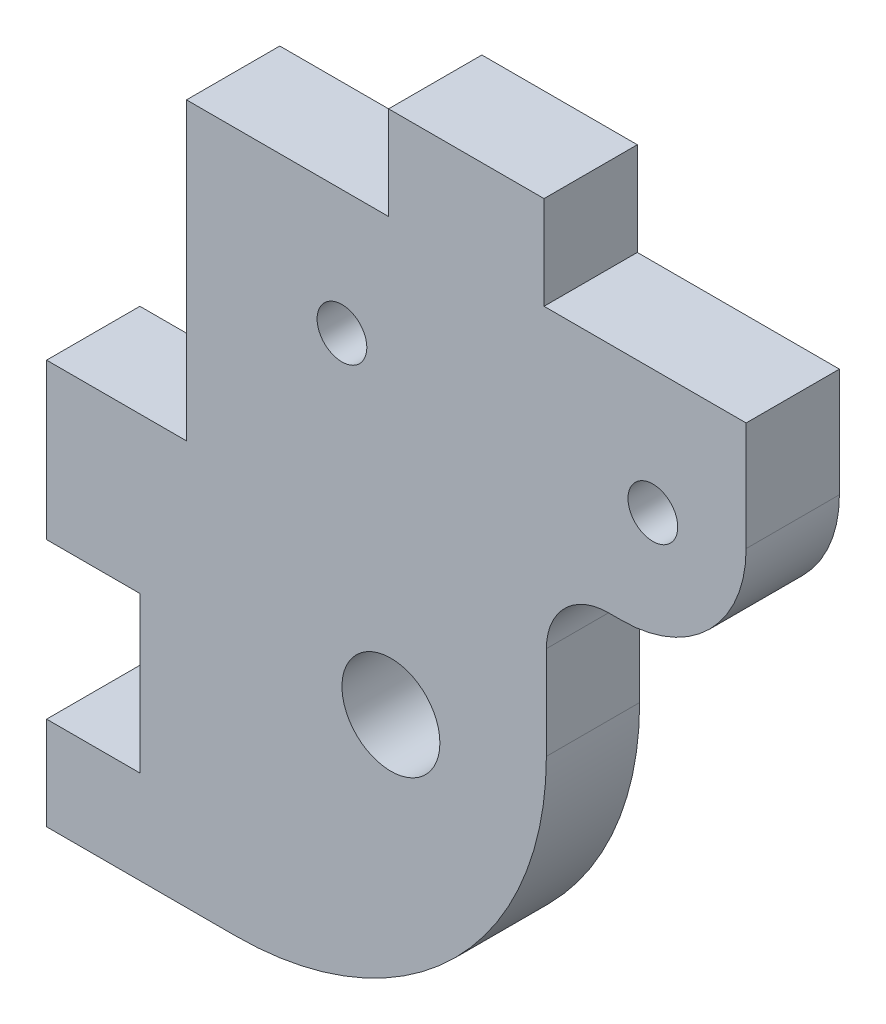
SolidWorks part; units mm, degrees
material "MDF"
ref_plane "Plano frontal" through (0, 0, 0) normal (0, 0, 1) x (1, 0, 0)
ref_plane "Plano superior" through (0, 0, 0) normal (0, 1, 0) x (1, 0, 0)
ref_plane "Plano direito" through (0, 0, 0) normal (1, 0, 0) x (0, 0, -1)
sketch "Esboço1" plane through (0, 0, 0) normal (0, 0, 1) x (1, 0, 0)
  line L5 (0, 0) -> (45, 0)
  line L10 (12.3685, -29.76) -> (16.2251, -47.9036) construction
  line L11 (16.2251, -47.9036) -> (21.3114, -46.8225) construction
  line L12 (21.3114, -46.8225) -> (22.15, -27.6808) construction
  line L13 (22.15, -27.6808) -> (12.3685, -29.76) construction
  line L14 (45, 0) -> (45, -45)
  line L15 (45, -45) -> (0, -45)
  line L16 (0, -45) -> (0, 0)
  line L17 (22.5, 0) -> (22.5, -45) construction
  line L18 (22.15, -27.6808) -> (16.2251, -47.9036) construction
  line L19 (22.15, -27.6808) -> (15.0789, -34.7519) construction
  line L20 (15.0789, -34.7519) -> (28.1951, -47.868) construction
  line L21 (28.1951, -47.868) -> (31.872, -44.1911) construction
  line L22 (19, -8) -> (16.2251, -47.9036) construction
  line L25 (19, -8) -> (39, -8) construction
  line L27 (32.15, -45) -> (32.15, -15)
  line L47 (32, 6) -> (22, 6)
  line L48 (32, 6) -> (32, 0)
  line L49 (32, 0) -> (22, 0)
  line L50 (22, 6) -> (22, 0)
  line L51 (9, -3.4599) -> (45, -3.4599) construction
  line L52 (32, 3) -> (22, 3) construction
  line L54 (6, -39) -> (0, -39)
  line L56 (6, -39) -> (6, -29)
  line L60 (6, -29) -> (0, -29)
  line L61 (0, -39) -> (0, -29)
  line L62 (6, -39) -> (0, -29) construction
  line L63 (6, -29) -> (0, -39) construction
  line L64 (32.15, -15) -> (45, -15)
  line L65 (0, -19) -> (9, -19)
  line L66 (9, -19) -> (9, 0)
  circle A0 centre (22.15, -27.6808) radius 3.15
  circle A1 centre (22.15, -27.6808) radius 22.85 construction
  circle A3 centre (39, -8) radius 1.6
  circle A4 centre (19, -8) radius 1.6
  circle A15 centre (39, -8) radius 3 construction
  circle A16 centre (22.15, -27.6808) radius 10 construction
  point P5 (45, -27.6808)
  point P8 (3, -34)
  point P11 (19, -27.6808)
  point P25 (25.3, -27.6808)
  point P31 (27, 3)
  point P40 (27, -3.4599)
  dimension "D3" = 6.3
  dimension "D6" = 10
  dimension "D11" = 10
  dimension "D19" = 6
  dimension "D18" = 8
  dimension "D10" = 6
  dimension "D21" = 6
  dimension "D23" = 20
  dimension "D15" = 6
  dimension "D13" = 3.2
  dimension "D4" = 19.16
  dimension "D5" = 5.2
  dimension "D7" = 12
  dimension "D8" = 40
  dimension "D9" = 19
  dimension "D12" = 45
  dimension "D14" = 34
  dimension "D16" = 19
  dimension "D17" = 20
  dimension "D20" = 10
  dimension "D22" = 45
  dimension "D24" = 7
  dimension "D25" = 10
  dimension "D26" = 10
  dimension "D27" = 9
extrude "Ressalto-extrusão1" add sketch "Esboço1" along normal blind 6
fillet "Filete2" radius 8 1 edges at (45, -15, 3)
fillet "Filete3" radius 4 1 edges at (32.15, -15, 3)
fillet "Filete4" radius 20 1 edges at (32.15, -45, 3)
